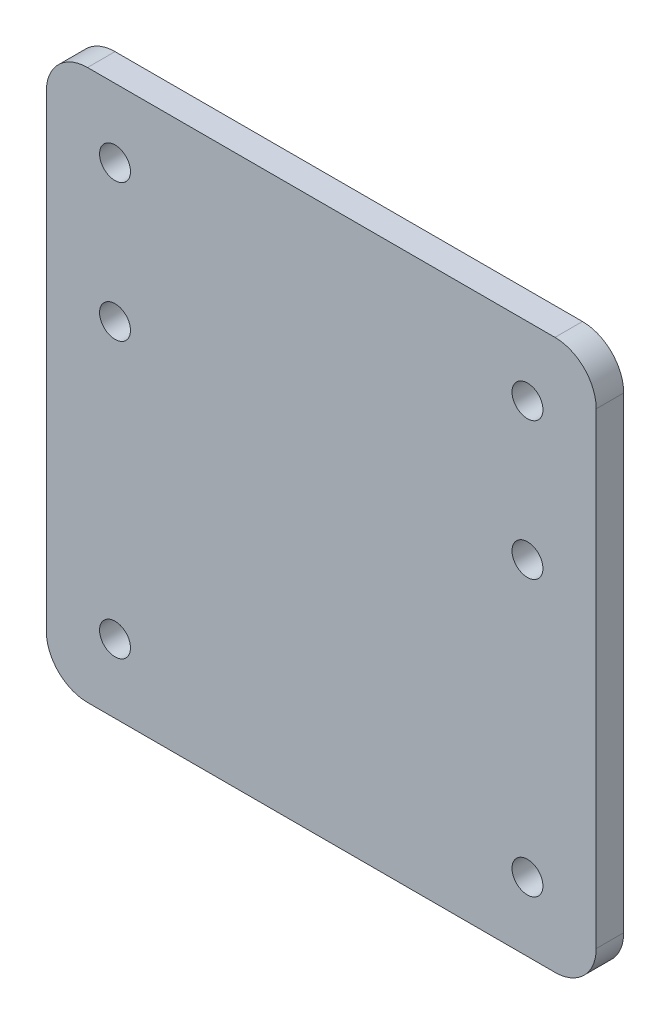
SolidWorks part; units mm, degrees
ref_plane "Front Plane" through (0, 0, 0) normal (0, 0, 1) x (1, 0, 0)
ref_plane "Top Plane" through (0, 0, 0) normal (0, 1, 0) x (1, 0, 0)
ref_plane "Right Plane" through (0, 0, 0) normal (1, 0, 0) x (0, 0, -1)
sketch "Sketch1" plane through (0, 0, 0) normal (0, 0, 1) x (1, 0, 0)
  line L0 (-34, -40) -> (34, -40)
  line L1 (40, -34) -> (40, 34)
  line L2 (34, 40) -> (-34, 40)
  line L3 (-40, 34) -> (-40, -34)
  circle A0 centre (-30, 10) radius 2.25
  circle A1 centre (30, -30) radius 2.25
  circle A2 centre (30, 10) radius 2.25
  circle A3 centre (-30, 30) radius 2.25
  circle A4 centre (-30, -30) radius 2.25
  circle A5 centre (30, 30) radius 2.25
  arc A6 (-40, -34) -> (-34, -40) centre (-34, -34) ccw
  arc A7 (34, -40) -> (40, -34) centre (34, -34) ccw
  arc A8 (40, 34) -> (34, 40) centre (34, 34) ccw
  arc A9 (-34, 40) -> (-40, 34) centre (-34, 34) ccw
  dimension "D1" = 6
  dimension "D2" = 40
  dimension "D3" = 40
  dimension "D4" = 40
extrude "Boss-Extrude1" add sketch "Sketch1" along normal blind 4
